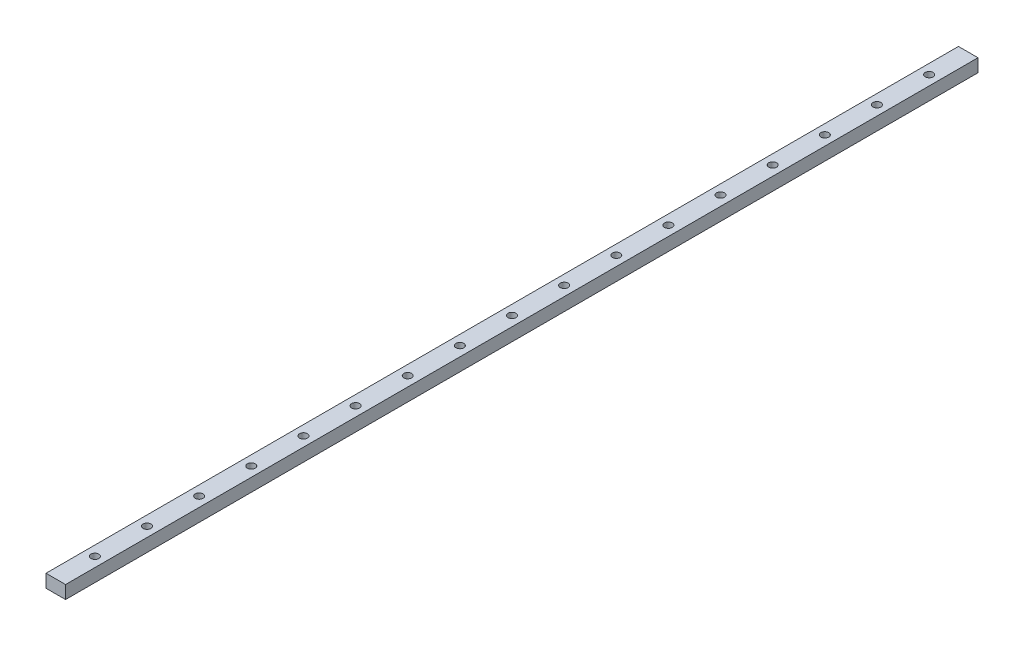
SolidWorks part; units mm, degrees
ref_plane "Front Plane" through (0, 0, 0) normal (0, 0, 1) x (1, 0, 0)
ref_plane "Top Plane" through (0, 0, 0) normal (0, 1, 0) x (1, 0, 0)
ref_plane "Right Plane" through (0, 0, 0) normal (1, 0, 0) x (0, 0, -1)
sketch "Sketch1" plane through (0, 0, 0) normal (0, 0, 1) x (1, 0, 0)
  line L1 (0, 0) -> (15, 0)
  line L2 (0, 0) -> (0, 10)
  line L3 (0, 10) -> (15, 10)
  line L4 (15, 0) -> (15, 10)
  dimension "D1" = 15
  dimension "D2" = 10
extrude "Boss-Extrude1" add sketch "Sketch1" along normal blind 700
hole_wizard "CBORE for M3 SHCS1" positions "Sketch2" profile "Sketch3" counterbore size "M3" standard "ANSI Metric" end condition through all
sketch "Sketch2" plane through (0, 10, 0) normal (0, 1, 0) x (1, 0, 0)
  line L0 (15, -700) -> (0, -700) construction
  line L1 (15, -700) -> (15, 0) construction
  point P0 (7.5, -670)
  dimension "D1" = 30
  dimension "D2" = 7.5
sketch "Sketch3" plane through (7.5, 10, 670) normal (1, 0, 0) x (0, 0, 1)
  line L0 (0, 0) -> (0, 10)
  line L1 (0, 10) -> (1.75, 10)
  line L3 (1.75, 10) -> (1.75, 4.5)
  line L4 (1.75, 4.5) -> (3, 4.5)
  line L5 (3, 4.5) -> (3, 0)
  line L7 (3, 0) -> (0, 0)
  line L11 (0, -6.35) -> (0, 107.95) construction
  dimension "Thru Hole Dia." = 3.5
  dimension "Thru Hole Depth" = 10
  dimension "C'Bore Dia." = 6
  dimension "C'Bore Depth" = 4.5
pattern_linear "LPattern1" count 17 spacing 40 along (0, 0, -1) of "CBORE for M3 SHCS1"
